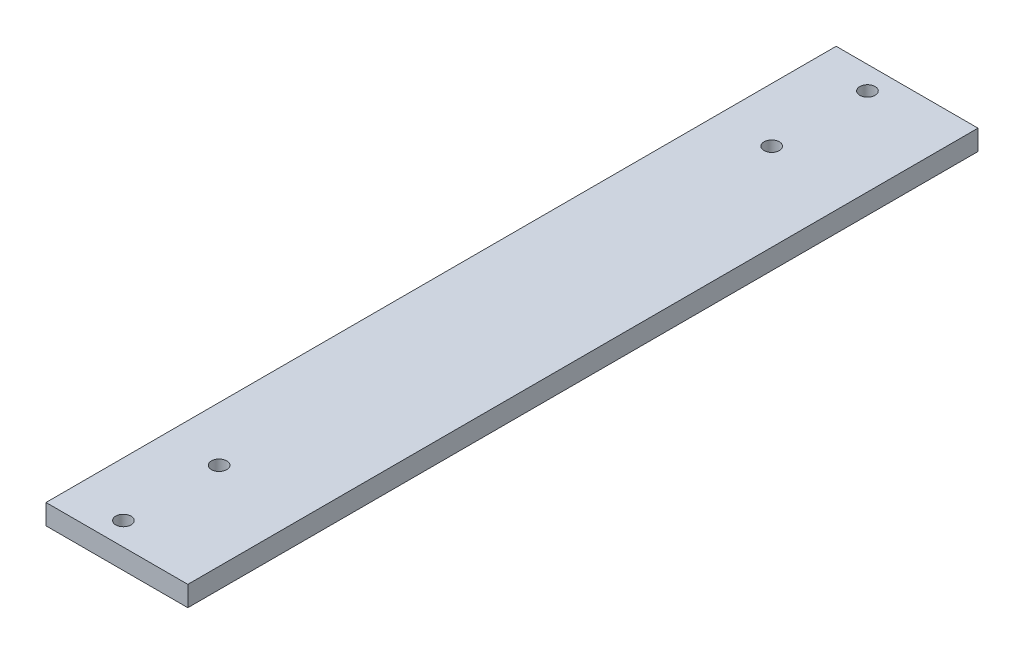
SolidWorks part; units mm, degrees
ref_plane "Front Plane" through (0, 0, 0) normal (0, 0, 1) x (1, 0, 0)
ref_plane "Top Plane" through (0, 0, 0) normal (0, 1, 0) x (1, 0, 0)
ref_plane "Right Plane" through (0, 0, 0) normal (1, 0, 0) x (0, 0, -1)
sketch "Sketch1" plane through (0, 0, 0) normal (0, 1, 0) x (1, 0, 0)
  line L1 (-22.225, -123.825) -> (22.225, -123.825)
  line L2 (-22.225, -123.825) -> (-22.225, 123.825)
  line L3 (-22.225, 123.825) -> (22.225, 123.825)
  line L4 (22.225, -123.825) -> (22.225, 123.825)
  line L5 (-22.225, -123.825) -> (22.225, 123.825) construction
  line L6 (-22.225, 123.825) -> (22.225, -123.825) construction
  point P0 (0, 0)
  dimension "D1" = 247.65
  dimension "D2" = 44.45
extrude "Boss-Extrude1" add sketch "Sketch1" along normal blind 6.35
hole_wizard "M4 Clearance Hole1" positions "Sketch3" profile "Sketch4" hole size "M4" standard "ANSI Metric" end condition through all
sketch "Sketch3" plane through (0, 0, 0) normal (0, -1, 0) x (-1, 0, 0)
  circle A0 centre (5.2, 86.6) radius 2.1 construction
  circle A1 centre (5.2, 116.6) radius 2.1 construction
  circle A2 centre (37.2, 116.6) radius 2.1 construction
  circle A3 centre (37.2, 86.6) radius 2.1 construction
  circle A4 centre (5.2, -116.6) radius 2.1 construction
  circle A5 centre (5.2, -86.6) radius 2.1 construction
  circle A6 centre (37.2, -86.6) radius 2.1 construction
  circle A7 centre (37.2, -116.6) radius 2.1 construction
  circle A8 centre (5.2, 86.6) radius 2.1 construction
  circle A9 centre (5.2, 116.6) radius 2.1 construction
  circle A10 centre (37.2, 116.6) radius 2.1 construction
  circle A11 centre (37.2, 86.6) radius 2.1 construction
  circle A12 centre (5.2, -116.6) radius 2.1 construction
  circle A13 centre (5.2, -86.6) radius 2.1 construction
  circle A14 centre (37.2, -86.6) radius 2.1 construction
  circle A15 centre (37.2, -116.6) radius 2.1 construction
  point P26 (37.2, -116.6)
  point P28 (5.2, -116.6)
  point P30 (5.2, -86.6)
  point P32 (37.2, -86.6)
  point P65 (37.2, 86.6)
  point P68 (37.2, 116.6)
  point P71 (5.2, 116.6)
  point P74 (5.2, 86.6)
sketch "Sketch4" plane through (-37.2, 0, 116.6) normal (1, 0, 0) x (0, 0, -1)
  line L0 (0, 0) -> (0, 6.35)
  line L1 (0, 6.35) -> (2.4, 6.35)
  line L2 (2.4, 6.35) -> (2.4, 0)
  line L5 (2.4, 0) -> (0, 0)
  line L11 (0, -6.35) -> (0, 107.95) construction
  dimension "Thru Hole Dia." = 4.8
  dimension "Thru Hole Depth" = 6.35
equation "\"length\"= 9.75in"
equation "\"width\"= 1.75in"
equation "\"thick\"= .25in"
equation "\"D1@Boss-Extrude1\"= \"thick\""
equation "\"D1@Sketch1\"=\"length\""
equation "\"D2@Sketch1\"=\"width\""
